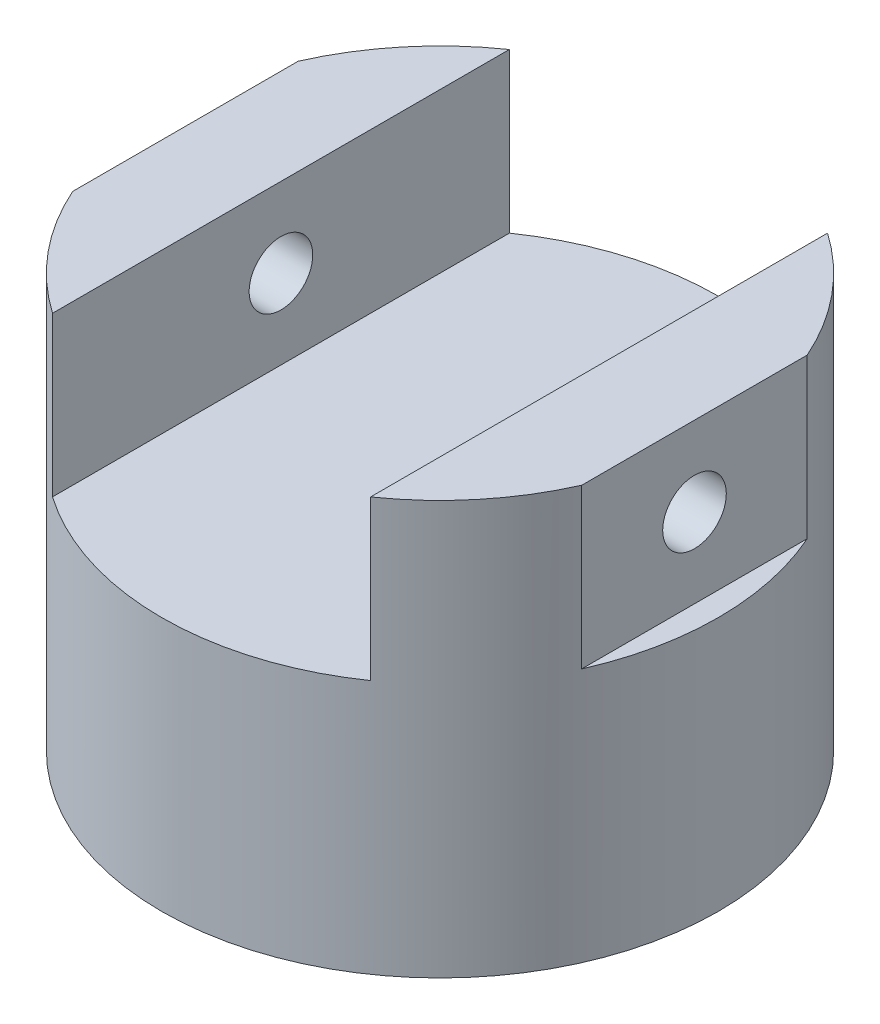
SolidWorks part; units mm, degrees
ref_plane "Plano frontal" through (0, 0, 0) normal (0, 0, 1) x (1, 0, 0)
ref_plane "Plano superior" through (0, 0, 0) normal (0, 1, 0) x (1, 0, 0)
ref_plane "Plano direito" through (0, 0, 0) normal (1, 0, 0) x (0, 0, -1)
sketch "Esboço1" plane through (0, 0, 0) normal (0, 0, 1) x (1, 0, 0)
  line L0 (0, 0) -> (0, 323.5206) construction
  line L1 (0, 0) -> (409.5885, 0) construction
  line L2 (0, 260) -> (175, 260)
  line L3 (175, 260) -> (175, 0)
  line L4 (175, 0) -> (0, 0)
  line L5 (0, 0) -> (0, 260)
  dimension "D1" = 350
  dimension "D2" = 260
revolve "Revolução1" add sketch "Esboço1" angle 360 about L0
sketch "Esboço2" plane through (0, 0, 0) normal (0, 0, 1) x (1, 0, 0)
  line L0 (0, 0) -> (0, 260) construction
  line L1 (175, 260) -> (-175, 260) construction
  line L2 (100, 260) -> (100, 160)
  line L3 (100, 160) -> (-100, 160)
  line L4 (160, 260) -> (160, 160)
  line L5 (160, 160) -> (175, 160)
  line L6 (175, 0) -> (175, 260) construction
  line L7 (175, 160) -> (175, 260)
  line L8 (175, 260) -> (160, 260)
  line L9 (100, 160) -> (160, 160) construction
  line L10 (100, 260) -> (-100, 260)
  line L11 (-175, 260) -> (-160, 260)
  line L12 (-175, 160) -> (-175, 260)
  line L13 (-160, 160) -> (-175, 160)
  line L14 (-160, 260) -> (-160, 160)
  line L15 (-100, 160) -> (-160, 160) construction
  line L16 (-100, 260) -> (-100, 160)
  point P20 (0, 160)
  dimension "D1" = 200
  dimension "D2" = 320
  dimension "D3" = 100
extrude "Corte-extrusão1" cut sketch "Esboço2" against normal through all both and the other way through all
sketch "Esboço3" plane through (160, 0, 0) normal (1, 0, 0) x (0, 0, -1)
  line L0 (0, 260) -> (0, 160) construction
  line L1 (70.8872, 260) -> (-70.8872, 260) construction
  line L2 (70.8872, 160) -> (-70.8872, 160) construction
  circle A0 centre (0, 210) radius 20
  dimension "D1" = 40
extrude "Corte-extrusão2" cut sketch "Esboço3" against normal through all both and the other way through all
